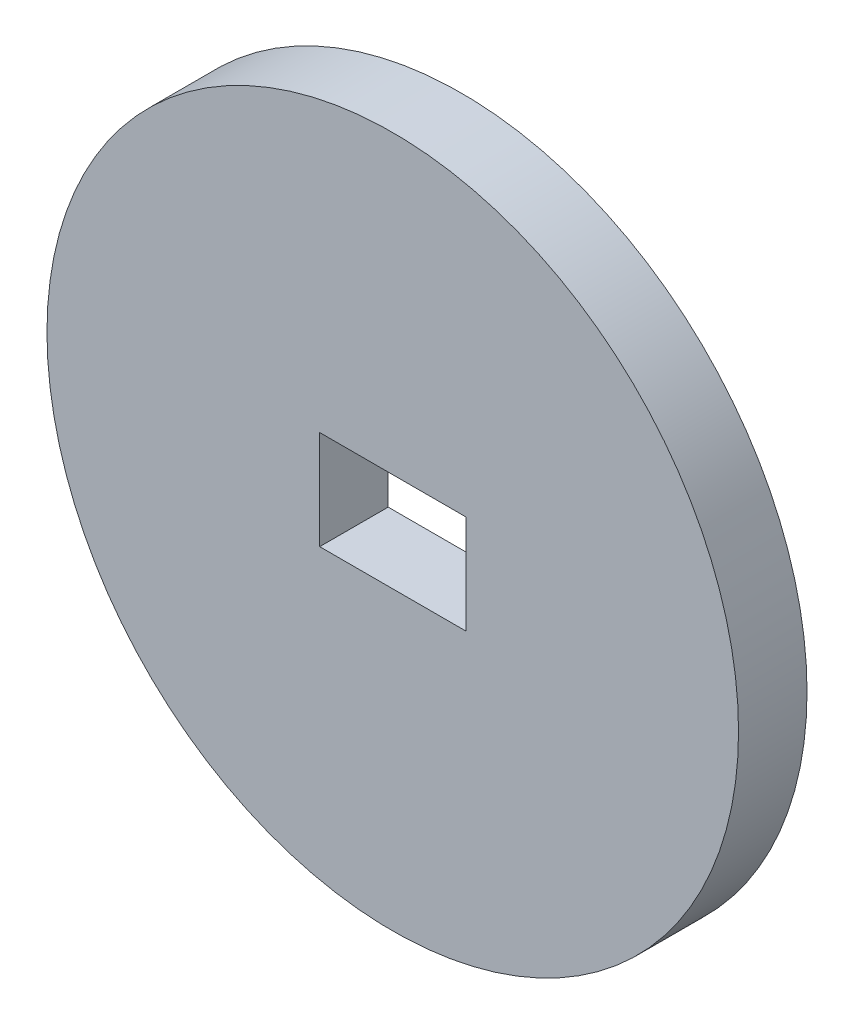
SolidWorks part; units mm, degrees
ref_plane "Front Plane" through (0, 0, 0) normal (0, 0, 1) x (1, 0, 0)
ref_plane "Top Plane" through (0, 0, 0) normal (0, 1, 0) x (1, 0, 0)
ref_plane "Right Plane" through (0, 0, 0) normal (1, 0, 0) x (0, 0, -1)
sketch "Sketch1" plane through (0, 0, 0) normal (0, 0, 1) x (1, 0, 0)
  circle A0 centre (0, 0) radius 12.875
  dimension "D1" = 25.75
extrude "Boss-Extrude1" add sketch "Sketch1" along normal blind 2.55
sketch "Sketch2" plane through (0, 0, 0) normal (0, 0, 1) x (1, 0, 0)
  line L1 (-2.72, -1.84) -> (2.72, -1.84)
  line L2 (-2.72, -1.84) -> (-2.72, 1.84)
  line L3 (-2.72, 1.84) -> (2.72, 1.84)
  line L4 (2.72, -1.84) -> (2.72, 1.84)
  line L5 (-2.72, -1.84) -> (2.72, 1.84) construction
  line L6 (-2.72, 1.84) -> (2.72, -1.84) construction
  point P0 (0, 0)
  dimension "D1" = 3.68
  dimension "D2" = 5.44
extrude "Cut-Extrude1" cut sketch "Sketch2" along normal up to surface (2.55 mm away) up to face at (12.875, 0, 2.55)
